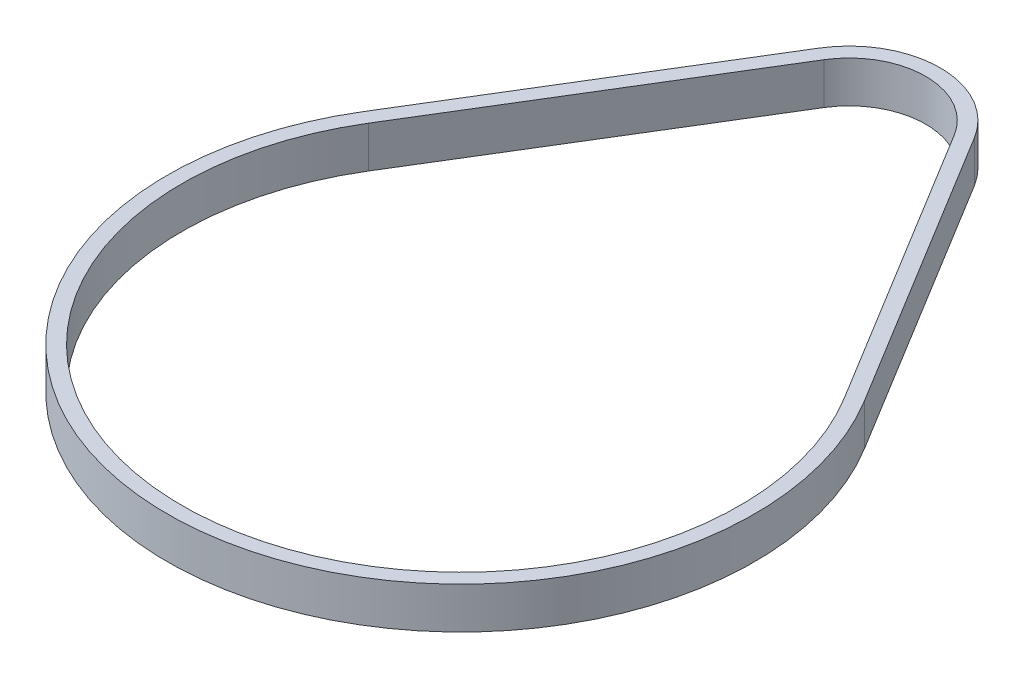
SolidWorks part; units mm, degrees
ref_plane "Front Plane" through (0, 0, 0) normal (0, 0, 1) x (1, 0, 0)
ref_plane "Top Plane" through (0, 0, 0) normal (0, 1, 0) x (1, 0, 0)
ref_plane "Right Plane" through (0, 0, 0) normal (1, 0, 0) x (0, 0, -1)
other "Bounding Box"
ref_plane "Default Plane" through (-8.9266, -12.7485, 0) normal (-0.1736, 0.9848, 0) x (0.9848, 0.1736, 0)
sketch "Sketch1" plane through (0, 0, 0) normal (0, 1, 0) x (1, 0, 0)
  line L0 (0, 0) -> (0, 84.2675) construction
  line L1 (-51.6473, 31.5629) -> (-14.1526, 92.9166)
  line L2 (14.1526, 92.9166) -> (51.6473, 31.5629)
  line L3 (-54.3565, 33.2186) -> (-16.8618, 94.5722)
  line L4 (16.8618, 94.5722) -> (54.3565, 33.2186)
  line L5 (-51.6473, 31.5629) -> (-54.3565, 33.2186) construction
  arc A0 (-51.6473, 31.5629) -> (51.6473, 31.5629) centre (0, 0) ccw
  arc A1 (14.1526, 92.9166) -> (-14.1526, 92.9166) centre (0, 84.2675) ccw
  arc A2 (-54.3565, 33.2186) -> (54.3565, 33.2186) centre (0, 0) ccw
  arc A3 (-16.8618, 94.5722) -> (16.8618, 94.5722) centre (0, 84.2675) cw
  dimension "D2" = 121.0564
  dimension "D3" = 16.5862
  dimension "D1" = 84.2675
  dimension "D4" = 3.175
extrude "Boss-Extrude1" add sketch "Sketch1" along normal blind 9
